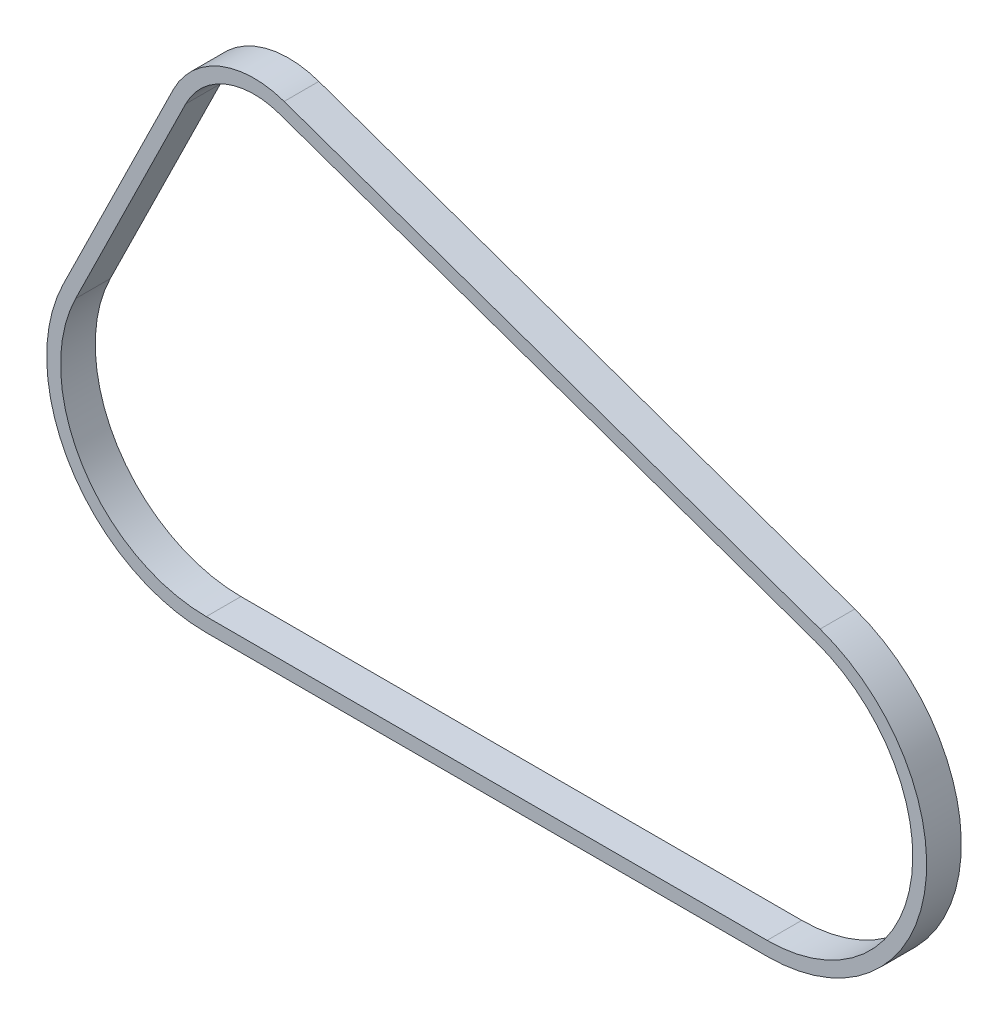
SolidWorks part; units mm, degrees
ref_plane "Front Plane" through (0, 0, 0) normal (0, 0, 1) x (1, 0, 0)
ref_plane "Top Plane" through (0, 0, 0) normal (0, 1, 0) x (1, 0, 0)
ref_plane "Right Plane" through (0, 0, 0) normal (1, 0, 0) x (0, 0, -1)
sketch "Sketch2" plane through (0, 0, 0) normal (0, 0, 1) x (1, 0, 0)
  line L0 (0, 0) -> (1, 0) construction
  line L1 (0, 0) -> (0, 1) construction
  line L2 (-29.6067, 14.5755) -> (-77.2369, -82.174)
  line L3 (-20.7151, -173) -> (221.8191, -173)
  line L4 (242.7633, -50.5833) -> (10.9708, 31.123)
  arc A0 (10.9708, 31.123) -> (-29.6067, 14.5755) centre (0, 0) ccw
  arc A1 (-77.2369, -82.174) -> (-20.7151, -173) centre (-20.7151, -110) ccw
  arc A2 (221.8191, -173) -> (242.7633, -50.5833) centre (221.8191, -110) ccw
extrude "Extrude-Thin1" add sketch "Sketch2" along normal blind 7.5 and the other way blind 7.5 thin
